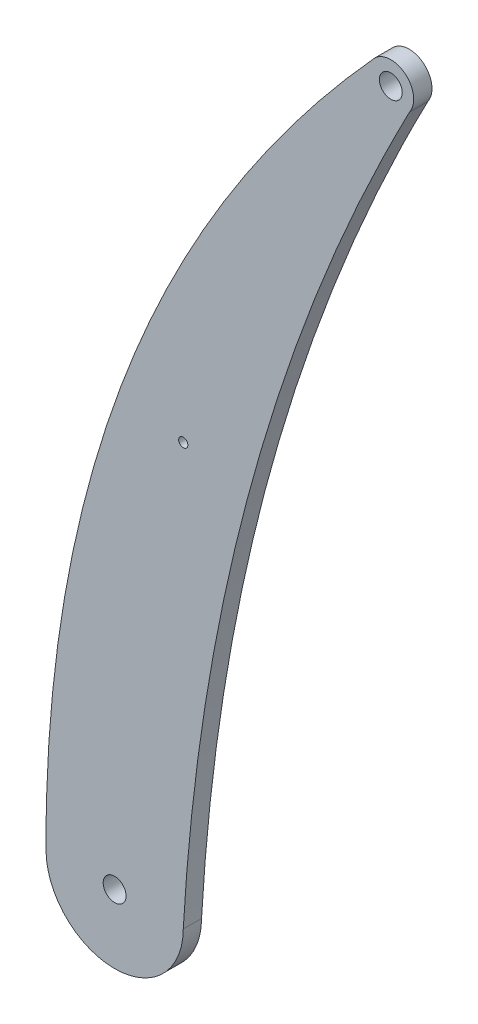
SolidWorks part; units mm, degrees
material "Cedar"
ref_plane "Front Plane" through (0, 0, 0) normal (0, 0, 1) x (1, 0, 0)
ref_plane "Top Plane" through (0, 0, 0) normal (0, 1, 0) x (1, 0, 0)
ref_plane "Right Plane" through (0, 0, 0) normal (1, 0, 0) x (0, 0, -1)
sketch "Sketch1" plane through (0, 0, 0) normal (0, 0, 1) x (1, 0, 0)
  line L0 (-33.3036, 15.3879) -> (18.6558, 15.3879) construction
  line L1 (18.6558, 15.3879) -> (18.6558, -184.6121) construction
  line L2 (-78.8442, 10.3879) -> (-34.221, -82.2618) construction
  circle A0 centre (11.1558, 7.8879) radius 2.5
  arc A1 (15.2542, 5.0237) -> (7.6042, 11.4072) centre (11.1558, 7.8879) ccw
  circle A2 centre (-78.8442, 10.3879) radius 1 construction
  circle A3 centre (-34.221, -82.2618) radius 1
  circle A4 centre (-49.221, -174.3885) radius 50 construction
  arc A5 (-64.221, -174.3885) -> (-34.221, -174.3885) centre (-49.221, -174.3885) ccw
  circle A6 centre (-49.221, -174.3885) radius 2.5
  spline S0 degree 2 poles (7.6042, 11.4072) (-64.6243, -68.0961) (-64.221, -174.3885) knots 0 0 0 1 1 1
  spline S1 degree 2 poles (15.2542, 5.0237) (-28.8246, -79.3549) (-34.221, -174.3885) knots 0 0 0 1 1 1
  spline S2 degree 2 poles (11.1558, 7.8879) (-47.0945, -74.1416) (-49.221, -174.3885) knots 0 0 0 1 1 1 construction
  point P13 (0, 0)
  dimension "D1" = 5
  dimension "D3" = 7.5
  dimension "D4" = 10
  dimension "D5" = 2
  dimension "D6" = 2
  dimension "D11" = 100
  dimension "D12" = 30
  dimension "D13" = 5
  dimension "D14" = 15
  dimension "D2" = 7.5
  dimension "D7" = 5
  dimension "D8" = 102.8358
  dimension "D9" = 90
  dimension "D10" = 200
  dimension "D15" = 15
extrude "Boss-Extrude1" add sketch "Sketch1" along normal blind 4
